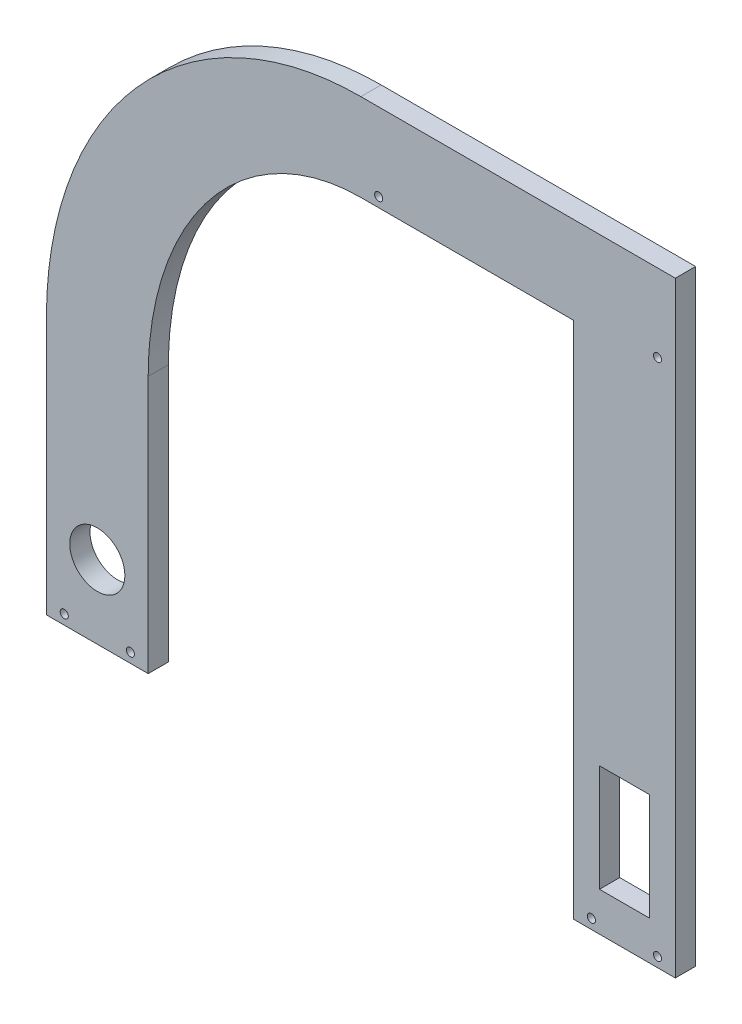
SolidWorks part; units mm, degrees
ref_plane "Front Plane" through (0, 0, 0) normal (0, 0, 1) x (1, 0, 0)
ref_plane "Top Plane" through (0, 0, 0) normal (0, 1, 0) x (1, 0, 0)
ref_plane "Right Plane" through (0, 0, 0) normal (1, 0, 0) x (0, 0, -1)
sketch "Sketch2" plane through (0, 0, 0) normal (0, 0, 1) x (1, 0, 0)
  line L1 (0, 0) -> (246.38, 0)
  line L2 (0, 0) -> (0, 254)
  line L3 (0, 254) -> (246.38, 254)
  line L4 (246.38, 0) -> (246.38, 254)
  dimension "D1" = 246.38
  dimension "D2" = 254
extrude "Boss-Extrude1" add sketch "Sketch2" along normal blind 7.9375
sketch "Sketch3" plane through (0, 0, 7.9375) normal (0, 0, 1) x (1, 0, 0)
  line L0 (0, 254) -> (0, 100.8751)
  line L1 (0, 0) -> (246.38, 0) construction
  line L2 (39.878, 0) -> (39.878, 100.8751)
  line L4 (206.502, 160.2846) -> (206.502, 0)
  line L5 (206.502, 0) -> (39.878, 0)
  line L6 (0, 254) -> (0, 0) construction
  line L7 (246.38, 0) -> (246.38, 254) construction
  line L8 (0, 254) -> (246.38, 254)
  line L9 (246.38, 254) -> (246.38, 237.4225)
  line L10 (123.19, 203.2) -> (206.502, 203.2)
  line L11 (206.502, 203.2) -> (206.502, 160.2846)
  line L12 (123.19, 237.4225) -> (246.38, 237.4225)
  ellipse E0 centre (123.19, 100.8751) end of major axis (123.19, 203.2) minor radius 83.312 (39.878, 100.8751) -> (123.19, 203.2) cw
  ellipse E1 centre (123.19, 100.8751) end of major axis (123.19, 237.4225) minor radius 123.19 (0, 100.8751) -> (123.19, 237.4225) cw
  point P12 (-0.7936, 100.8751)
  dimension "D1" = 39.878
  dimension "D2" = 39.878
  dimension "D4" = 123.19
extrude "Cut-Extrude2" cut sketch "Sketch3" against normal up to next
sketch "Sketch4" plane through (0, 0, 7.9375) normal (0, 0, 1) x (1, 0, 0)
  line L5 (0, 0) -> (39.878, 0) construction
  line L6 (0, 100.8751) -> (0, 0) construction
  line L7 (39.878, 100.8751) -> (39.878, 0) construction
  line L8 (206.502, 0) -> (206.502, 203.2) construction
  line L9 (246.38, 0) -> (246.38, 237.4225) construction
  line L10 (206.502, 0) -> (246.38, 0) construction
  line L12 (206.502, 203.2) -> (123.19, 203.2) construction
  circle A0 centre (6.985, 3.81) radius 1.5875
  circle A1 centre (32.893, 3.81) radius 1.5875
  circle A2 centre (213.487, 3.81) radius 1.5875
  circle A3 centre (239.395, 3.81) radius 1.5875
  circle A4 centre (130.175, 207.01) radius 1.5875
  circle A5 centre (239.395, 207.01) radius 1.5875
  dimension "D2" = 3.175
  dimension "D3" = 3.175
  dimension "D7" = 3.175
  dimension "D8" = 3.175
  dimension "D14" = 3.175
  dimension "D15" = 3.175
  dimension "D1" = 3.81
  dimension "D4" = 3.81
  dimension "D5" = 6.985
  dimension "D6" = 6.985
  dimension "D9" = 6.985
  dimension "D10" = 6.985
  dimension "D11" = 3.81
  dimension "D12" = 3.81
  dimension "D13" = 3.81
  dimension "D16" = 3.81
  dimension "D17" = 6.985
  dimension "D18" = 6.985
extrude "screw holes" cut sketch "Sketch4" against normal up to next
sketch "Sketch5" plane through (0, 0, 7.9375) normal (0, 0, 1) x (1, 0, 0)
  circle A0 centre (19.939, 28.702) radius 10.795 construction
  circle A1 centre (19.939, 28.702) radius 10.795
extrude "Cut-Extrude4" cut sketch "Sketch5" against normal up to next
sketch "Sketch6" plane through (0, 0, 7.9375) normal (0, 0, 1) x (1, 0, 0)
  line L0 (206.502, 0) -> (246.38, 0) construction
  line L1 (236.22, 15.24) -> (216.662, 15.24)
  line L2 (236.22, 15.24) -> (236.22, 57.15)
  line L3 (236.22, 57.15) -> (216.662, 57.15)
  line L4 (216.662, 15.24) -> (216.662, 57.15)
  line L5 (206.502, 0) -> (206.502, 203.2) construction
  line L6 (246.38, 0) -> (246.38, 237.4225) construction
  dimension "D1" = 15.24
  dimension "D2" = 10.16
  dimension "D3" = 10.16
  dimension "D4" = 57.15
extrude "Cut-Extrude5" cut sketch "Sketch6" against normal up to next
